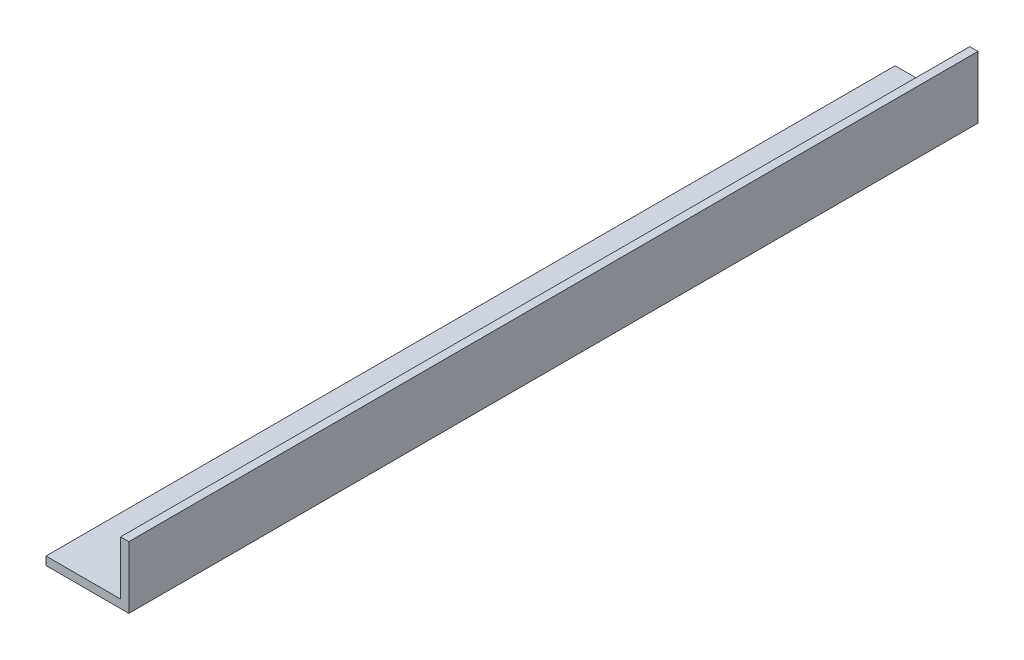
SolidWorks part; units mm, degrees
ref_plane "Ebene vorne" through (0, 0, 0) normal (0, 0, 1) x (1, 0, 0)
ref_plane "Ebene oben" through (0, 0, 0) normal (0, 1, 0) x (1, 0, 0)
ref_plane "Ebene rechts" through (0, 0, 0) normal (1, 0, 0) x (0, 0, -1)
sketch "Skizze1" plane through (0, 0, 0) normal (0, 0, 1) x (1, 0, 0)
  line L0 (0, 0) -> (20, 0)
  line L1 (20, 0) -> (20, 15)
  line L2 (20, 15) -> (18, 15)
  line L3 (18, 15) -> (18, 2)
  line L4 (18, 2) -> (0, 2)
  line L5 (0, 2) -> (0, 0)
  dimension "D1" = 2
  dimension "D2" = 2
  dimension "D3" = 20
  dimension "D4" = 15
extrude "Aufsatz-Linear austragen1" add sketch "Skizze1" along normal blind 205
